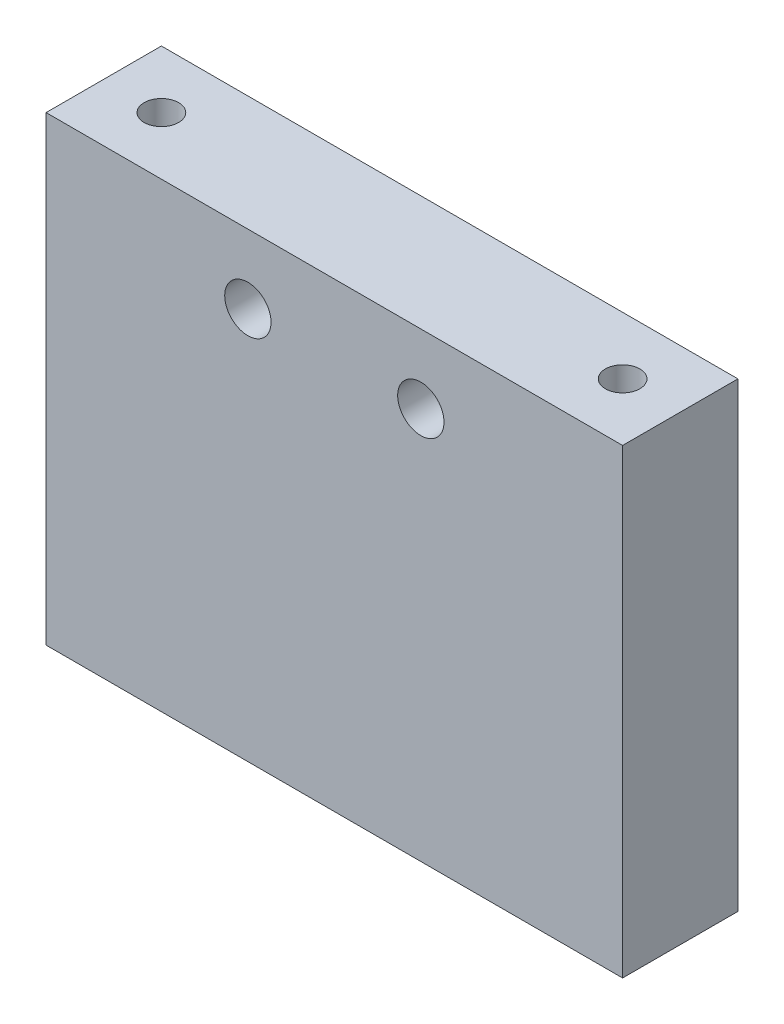
SolidWorks part; units mm, degrees
ref_plane "Front Plane" through (0, 0, 0) normal (0, 0, 1) x (1, 0, 0)
ref_plane "Top Plane" through (0, 0, 0) normal (0, 1, 0) x (1, 0, 0)
ref_plane "Right Plane" through (0, 0, 0) normal (1, 0, 0) x (0, 0, -1)
sketch "Sketch1" plane through (0, 0, 0) normal (0, 1, 0) x (1, 0, 0)
  line L1 (0, 0) -> (63.5, 0)
  line L2 (0, 0) -> (0, 12.7)
  line L3 (0, 12.7) -> (63.5, 12.7)
  line L4 (63.5, 0) -> (63.5, 12.7)
  dimension "D1" = 63.5
  dimension "D2" = 12.7
extrude "Boss-Extrude1" add sketch "Sketch1" along normal blind 50.8 contours L3 L4 L1 L2
hole_wizard "#25 (0.1495) Diameter Hole1" positions "Sketch2" profile "Sketch3" hole size "#25" standard "ANSI Inch"
sketch "Sketch2" plane through (0, 50.8, 0) normal (0, 1, 0) x (1, 0, 0)
  line L0 (31.75, 12.7) -> (31.75, 0) construction
  line L1 (0, 12.7) -> (63.5, 12.7) construction
  line L2 (0, 0) -> (63.5, 0) construction
  line L4 (0, 0) -> (0, 12.7) construction
  point P0 (6.35, 6.35)
  point P5 (6.35, 6.35)
  point P9 (6.35, 6.35)
  point P20 (0, 0)
  point P21 (57.15, 6.35)
  point P22 (0, 0)
  dimension "D1" = 6.35
  dimension "D2" = 6.35
sketch "Sketch3" plane through (6.35, 50.8, -6.35) normal (1, 0, 0) x (0, 0, 1)
  line L0 (0, 0) -> (0, 13.8408)
  line L1 (0, 13.8408) -> (1.8986, 12.7)
  line L2 (1.8986, 12.7) -> (1.8986, 0)
  line L5 (1.8986, 0) -> (0, 0)
  line L10 (0, 13.8408) -> (-1.8986, 12.7) construction
  line L11 (0, -6.35) -> (0, 107.95) construction
  dimension "Hole Dia." = 3.7973
  dimension "Hole Depth" = 12.7
  dimension "Drill Angle" = 118
hole_wizard "#7 (0.201) Diameter Hole1" positions "Sketch4" profile "Sketch5" hole size "#7" standard "ANSI Inch"
sketch "Sketch4" plane through (0, 0, -12.7) normal (0, 0, -1) x (-1, 0, 0)
  line L0 (-31.75, 50.8) -> (-31.75, 0) construction
  line L1 (0, 50.8) -> (-63.5, 50.8) construction
  line L2 (0, 0) -> (-63.5, 0) construction
  point P0 (-22.225, 43.18)
  point P11 (0, 0)
  point P12 (-41.275, 43.18)
  dimension "D1" = 19.05
  dimension "D2" = 7.62
sketch "Sketch5" plane through (22.225, 43.18, -12.7) normal (1, 0, 0) x (0, 1, 0)
  line L0 (0, 0) -> (0, 14.2338)
  line L1 (0, 14.2338) -> (2.5527, 12.7)
  line L2 (2.5527, 12.7) -> (2.5527, 0)
  line L5 (2.5527, 0) -> (0, 0)
  line L10 (0, 14.2338) -> (-2.5527, 12.7) construction
  line L11 (0, -6.35) -> (0, 107.95) construction
  dimension "Hole Dia." = 5.1054
  dimension "Hole Depth" = 12.7
  dimension "Drill Angle" = 118
